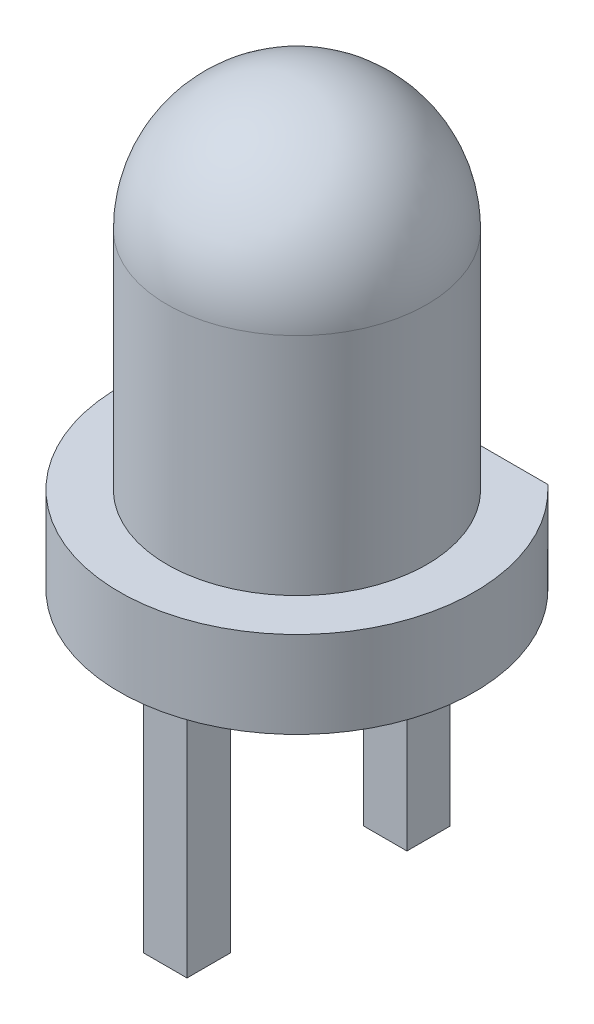
SolidWorks part; units mm, degrees
ref_plane "Front Plane" through (0, 0, 0) normal (0, 0, 1) x (1, 0, 0)
ref_plane "Top Plane" through (0, 0, 0) normal (0, 1, 0) x (1, 0, 0)
ref_plane "Right Plane" through (0, 0, 0) normal (1, 0, 0) x (0, 0, -1)
sketch "Sketch1" plane through (0, 0, 0) normal (0, 0, 1) x (1, 0, 0)
  line L0 (0, 9.2836) -> (0, -8.43) construction
  line L1 (-1.5, 2.6) -> (-1.5, 0)
  line L2 (-1.5, 0) -> (-2.05, 0)
  line L3 (-2.05, 0) -> (-2.05, -1)
  line L4 (-2.05, -1) -> (0, -1)
  line L5 (0, 4.1) -> (0, -1)
  arc A0 (0, 4.1) -> (-1.5, 2.6) centre (0, 2.6) ccw
  dimension "D1" = 3
  dimension "D2" = 1
  dimension "D3" = 5.1
  dimension "D4" = 4.1
revolve "Revolve1" add sketch "Sketch1" angle 360 about L5
sketch "Sketch2" plane through (0, 0, 0) normal (0, 1, 0) x (1, 0, 0)
  line L0 (-1.9494, 1.5) -> (2.0974, 1.5)
  line L1 (2.0974, 1.5) -> (0.5052, 3.4038)
  line L2 (0.5052, 3.4038) -> (-1.9494, 1.5)
extrude "Cut-Extrude1" cut sketch "Sketch2" against normal through all
sketch "Sketch3" plane through (0, -1, 0) normal (0, -1, 0) x (1, 0, 0)
  line L1 (-0.25, 1.02) -> (0.25, 1.02)
  line L2 (-0.25, 1.02) -> (-0.25, 1.52)
  line L3 (-0.25, 1.52) -> (0.25, 1.52)
  line L4 (0.25, 1.02) -> (0.25, 1.52)
  line L5 (-0.25, 1.02) -> (0.25, 1.52) construction
  line L6 (-0.25, 1.52) -> (0.25, 1.02) construction
  line L7 (-0.25, -1.52) -> (0.25, -1.52)
  line L8 (-0.25, -1.52) -> (-0.25, -1.02)
  line L9 (-0.25, -1.02) -> (0.25, -1.02)
  line L10 (0.25, -1.52) -> (0.25, -1.02)
  line L11 (-0.25, -1.52) -> (0.25, -1.02) construction
  line L12 (-0.25, -1.02) -> (0.25, -1.52) construction
  circle A0 centre (0, 0) radius 1.27 construction
  point P3 (0, 1.27)
  point P8 (0, -1.27)
  dimension "D1" = 2.54
  dimension "D2" = 0.5
extrude "Boss-Extrude1" add sketch "Sketch3" along normal blind 3
